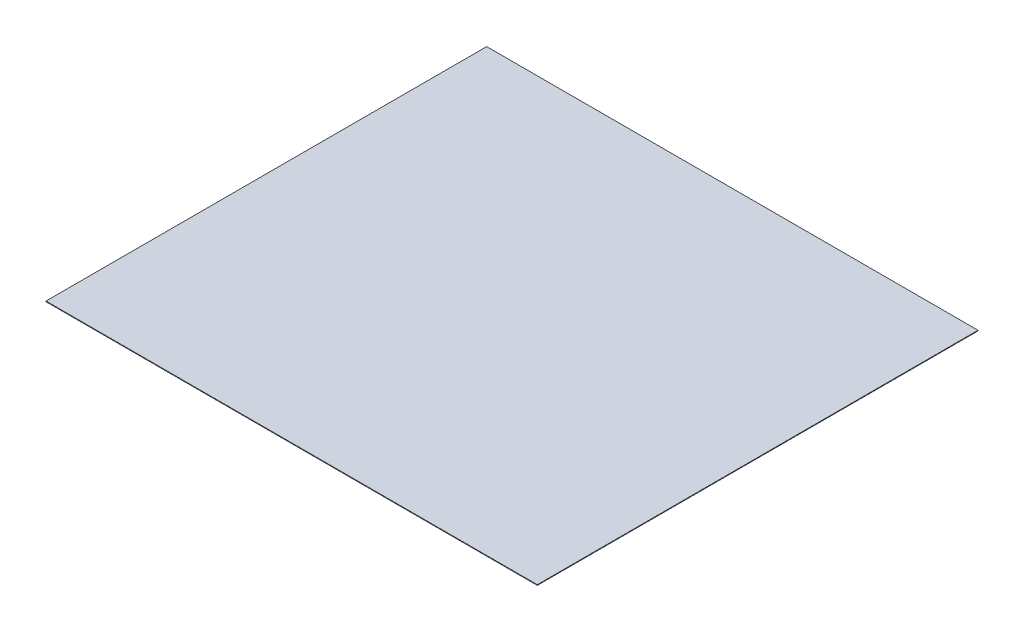
SolidWorks part; units mm, degrees
ref_plane "Front Plane" through (0, 0, 0) normal (0, 0, 1) x (1, 0, 0)
ref_plane "Top Plane" through (0, 0, 0) normal (0, 1, 0) x (1, 0, 0)
ref_plane "Right Plane" through (0, 0, 0) normal (1, 0, 0) x (0, 0, -1)
sketch "Sketch1" plane through (0, 0, 0) normal (0, 1, 0) x (1, 0, 0)
  line L1 (-3902, -3500) -> (3902, -3500)
  line L2 (-3902, -3500) -> (-3902, 3500)
  line L3 (-3902, 3500) -> (3902, 3500)
  line L4 (3902, -3500) -> (3902, 3500)
  line L5 (-3902, -3500) -> (3902, 3500) construction
  line L6 (-3902, 3500) -> (3902, -3500) construction
  point P0 (0, 0)
  dimension "D1" = 7804
  dimension "D2" = 7000
extrude "Boss-Extrude1" add sketch "Sketch1" along normal blind 10
